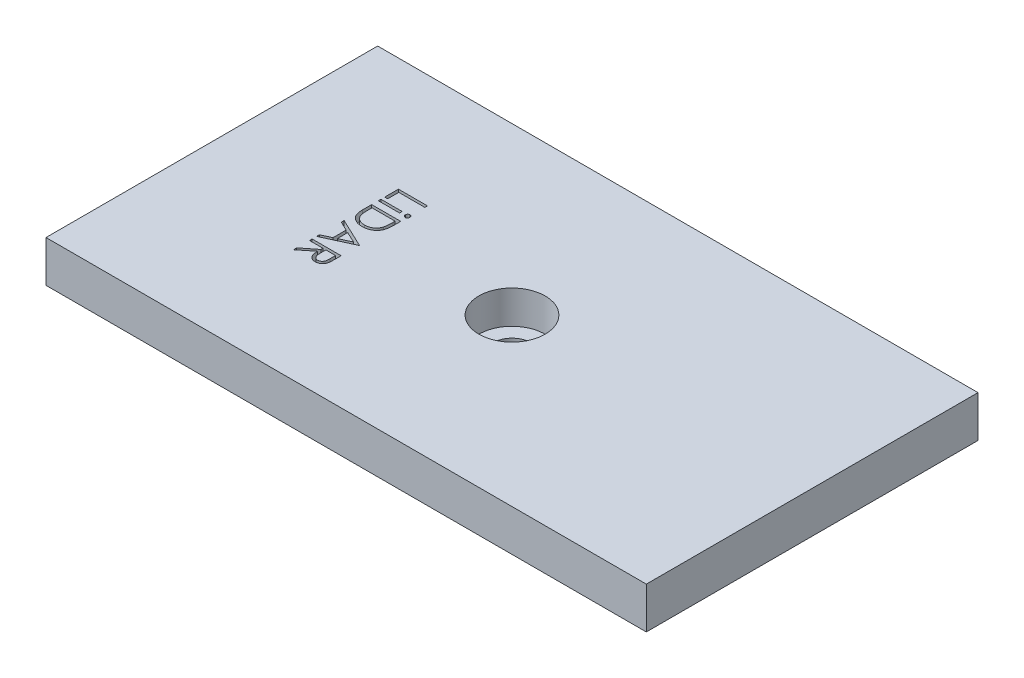
SolidWorks part; units mm, degrees
ref_plane "Front Plane" through (0, 0, 0) normal (0, 0, 1) x (1, 0, 0)
ref_plane "Top Plane" through (0, 0, 0) normal (0, 1, 0) x (1, 0, 0)
ref_plane "Right Plane" through (0, 0, 0) normal (1, 0, 0) x (0, 0, -1)
sketch "Sketch1" plane through (0, 0, 0) normal (0, 1, 0) x (1, 0, 0)
  line L1 (-36.2, 20) -> (36.2, 20)
  line L2 (-36.2, 20) -> (-36.2, -20)
  line L3 (-36.2, -20) -> (36.2, -20)
  line L4 (36.2, 20) -> (36.2, -20)
  line L5 (-36.2, 20) -> (36.2, -20) construction
  line L6 (-36.2, -20) -> (36.2, 20) construction
  point P0 (0, 0)
  dimension "D1" = 40
  dimension "D2" = 72.4
extrude "Boss-Extrude1" add sketch "Sketch1" along normal blind 6
chamfer "Chamfer1" distance 1 angle 45 4 edges at (0, 0, -20) (-36.2, 0, 0) (0, 0, 20) (36.2, 0, 0)
sketch "Sketch2" plane through (0, 6, 0) normal (0, 1, 0) x (1, 0, 0)
  line L0 (-36.2, 0) -> (36.2, 0) construction
  line L1 (-36.2, 20) -> (-36.2, -20) construction
  line L2 (36.2, -20) -> (36.2, 20) construction
  point P8 (0, 0)
hole_wizard "CBORE for M4 SHCS1" positions "Sketch2" profile "Sketch3" counterbore size "M4" standard "ANSI Metric" end condition up to next
sketch "Sketch3" plane through (0, 6, 0) normal (1, 0, 0) x (0, 0, 1)
  line L0 (0, 0) -> (0, 6)
  line L1 (0, 6) -> (2.25, 6)
  line L3 (2.25, 6) -> (2.25, 4)
  line L4 (2.25, 4) -> (4, 4)
  line L5 (4, 4) -> (4, 0)
  line L7 (4, 0) -> (0, 0)
  line L11 (0, -6.35) -> (0, 107.95) construction
  dimension "Thru Hole Dia." = 4.5
  dimension "Thru Hole Depth" = 6
  dimension "C'Bore Dia." = 8
  dimension "C'Bore Depth" = 4
sketch "Sketch4" plane through (0, 6, 0) normal (0, 1, 0) x (1, 0, 0)
  line L0 (-20, 20) -> (-20, -20) construction
  line L1 (36.2, 20) -> (-36.2, 20) construction
  line L2 (-36.2, -20) -> (36.2, -20) construction
  text T0 "LiDAR"
  dimension "D1" = 20
extrude "Cut-Extrude1" cut sketch "Sketch4" against normal blind 1
equation "\"Length\"=72.4"
equation "\"D2@Sketch1\"=\"Length\""
